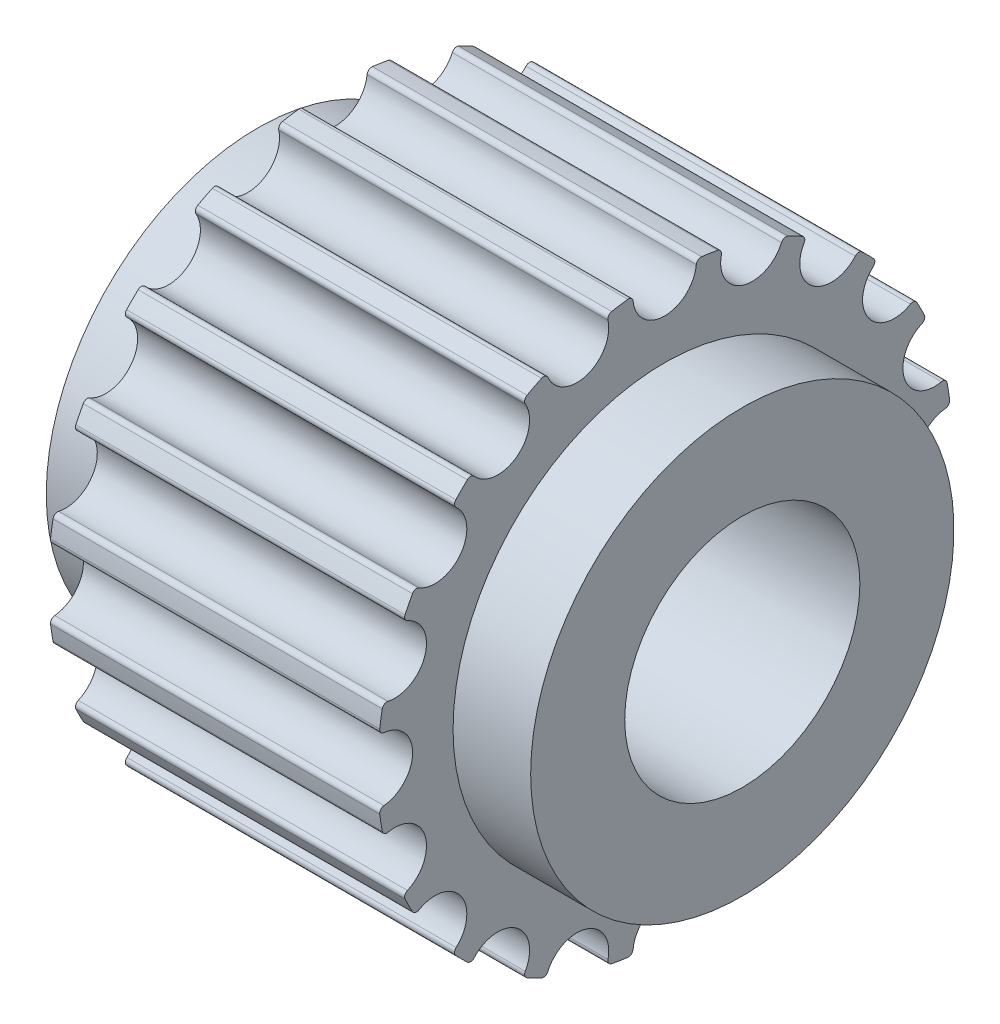
SolidWorks part; units mm, degrees
ref_plane "Front Plane" through (0, 0, 0) normal (0, 0, 1) x (1, 0, 0)
ref_plane "Top Plane" through (0, 0, 0) normal (0, 1, 0) x (1, 0, 0)
ref_plane "Right Plane" through (0, 0, 0) normal (1, 0, 0) x (0, 0, -1)
sketch "Sketch1" plane through (0, 0, 0) normal (0, 0, 1) x (1, 0, 0)
  line L0 (1.65, 6.365) -> (8.65, 6.365) construction
  line L1 (1.65, 6.11) -> (8.65, 6.11)
  line L2 (0, 4.5) -> (0, 2.5)
  line L4 (10.3, 4.5) -> (10.3, 2.5)
  line L5 (0, 2.5) -> (10.3, 2.5)
  line L6 (0, 0) -> (10.3, 0) construction
  line L8 (1.65, 4.5) -> (0, 4.5)
  line L9 (8.65, 4.5) -> (8.65, 6.11)
  line L10 (10.3, 4.5) -> (8.65, 4.5)
  line L13 (1.65, 4.5) -> (1.65, 6.11)
  dimension "W" = 10.3
  dimension "A" = 7
  dimension "E" = 9
  dimension "H" = 5
revolve "Revolve1" add sketch "Sketch1" angle 360 about L6
sketch "Sketch2" plane through (1.65, 0, 0) normal (1, 0, 0) x (0, 0, -1)
  line L0 (0, 0) -> (0, 6.11) construction
  circle A0 centre (0, 0) radius 6.11 construction
  circle A1 centre (0, 0) radius 6.11 construction
  arc A2 (0.6739, 6.0727) -> (-0.6739, 6.0727) centre (0, 0) ccw
  arc A3 (-0.6739, 6.0727) -> (0.6739, 6.0727) centre (0, 6.035) ccw
  circle A6 centre (0, 0) radius 5.36 construction
  circle A7 centre (0, 0) radius 6.364 construction
  dimension "MSM_3" = 0.675
  dimension "MSM_2" = 0.254
  dimension "MSM_1" = 0.75
extrude "Cut-Extrude1" cut sketch "Sketch2" along normal through all
fillet "Fillet1" radius 0.1 2 edges at (5.15, 6.0727, -0.6739) (5.15, 6.0727, 0.6739)
pattern_circular "CirPattern1" count 20 over 360 about axis through (0, 0, 0) along (1, 0, 0) of "Cut-Extrude1", "Fillet1"
hole_wizard "Tapped Hole2" [suppressed] positions "Sketch9" profile "Sketch8" tap size "M3x0.5" standard "JIS"
sketch "Sketch9" [suppressed] plane through (10.3, 8.8848, 0.534) normal (1, 0, 0) x (0, 0, -1)
  line L2 (0.534, -8.8848) -> (0.534, -16.8848) construction
  line L3 (0.534, -8.8848) -> (-6.3942, -4.8848) construction
  circle A0 centre (0.534, -8.8848) radius 8 construction
  point P0 (0.534, -16.8848)
  point P23 (-6.3942, -4.8848)
  point P24 (7.4622, -4.8848)
  dimension "QTC" = 16
  dimension "Angle_2" = 120
  dimension "Number" = 3
sketch "Sketch8" [suppressed] plane through (10.3, -8, 0) normal (0, 1, 0) x (0, 0, -1)
  line L0 (0, 0) -> (0, 9.2511)
  line L1 (0, 9.2511) -> (1.25, 8.5)
  line L2 (1.25, 8.5) -> (1.25, 0)
  line L5 (1.25, 0) -> (0, 0)
  line L10 (0, 9.2511) -> (-1.25, 8.5) construction
  line L11 (0, 0) -> (0, 9.2511) construction
  dimension "Tap Drill Dia." = 2.5
  dimension "Tap Drill Depth" = 8.5
  dimension "Drill Angle" = 118
cosmetic thread "Hole Thread2" [suppressed] parameters "Mx2"=6, "M"=3
cosmetic thread "Hole Thread3" [suppressed] parameters "Mx2"=6, "M"=3
cosmetic thread "Hole Thread4" [suppressed] parameters "Mx2"=6, "M"=3
hole_wizard "Tapped Hole3" [suppressed] positions "Sketch11" profile "Sketch10" tap size "M3x0.5" standard "JIS"
sketch "Sketch11" [suppressed] plane through (10.3, 6.1168, -5.003) normal (1, 0, 0) x (0, 0, -1)
  line L3 (-5.003, -6.1168) -> (-10.6598, -11.7737) construction
  line L4 (-5.003, -6.1168) -> (-10.6598, -0.46) construction
  line L5 (-5.003, 1.8832) -> (-5.003, -14.1168) construction
  circle A0 centre (-5.003, -6.1168) radius 8 construction
  point P22 (-10.6598, -11.7737)
  point P23 (6.0104, 6.0104)
  point P27 (-10.6598, -0.46)
  point P28 (0.6539, -0.46)
  point P29 (0.6539, -11.7737)
  dimension "QFC" = 16
  dimension "Angle_2" = 90
  dimension "Angle_1" = 45
  dimension "Number" = 4
sketch "Sketch10" [suppressed] plane through (10.3, -5.6569, 5.6569) normal (0, 1, 0) x (0, 0, -1)
  line L0 (0, 0) -> (0, 9.2511)
  line L1 (0, 9.2511) -> (1.25, 8.5)
  line L2 (1.25, 8.5) -> (1.25, 0)
  line L5 (1.25, 0) -> (0, 0)
  line L10 (0, 9.2511) -> (-1.25, 8.5) construction
  line L11 (0, 0) -> (0, 9.2511) construction
  dimension "Tap Drill Dia." = 2.5
  dimension "Tap Drill Depth" = 8.5
  dimension "Drill Angle" = 118
cosmetic thread "Hole Thread5" [suppressed] parameters "Mx2"=6, "M"=3
cosmetic thread "Hole Thread6" [suppressed] parameters "Mx2"=6, "M"=3
cosmetic thread "Hole Thread7" [suppressed] parameters "Mx2"=6, "M"=3
cosmetic thread "Hole Thread8" [suppressed] parameters "Mx2"=6, "M"=3
hole_wizard "Tapped Hole4" [suppressed] positions "Sketch13" profile "Sketch12" tap size "M3x0.5" standard "JIS"
sketch "Sketch13" [suppressed] plane through (10.3, 0, 0) normal (1, 0, 0) x (0, 0, -1)
  line L0 (0, 0) -> (0, 8) construction
  line L2 (0, 0) -> (-3.3809, 7.2505) construction
  line L4 (0, 0) -> (4.5886, 6.5532) construction
  circle A0 centre (0, 0) radius 8 construction
  point P0 (-3.3809, 7.2505)
  point P33 (4.5886, 6.5532)
  point P34 (7.9696, -0.6972)
  point P35 (3.3809, -7.2505)
  point P36 (-4.5886, -6.5532)
  point P37 (-7.9696, 0.6972)
  point P38 (0, 0)
  dimension "QSC" = 16
  dimension "Angle_1" = 35
  dimension "Angle_2" = 60
  dimension "Number" = 6
sketch "Sketch12" [suppressed] plane through (10.3, 7.2505, 3.3809) normal (0, 1, 0) x (0, 0, -1)
  line L0 (0, 0) -> (0, 9.2511)
  line L1 (0, 9.2511) -> (1.25, 8.5)
  line L2 (1.25, 8.5) -> (1.25, 0)
  line L5 (1.25, 0) -> (0, 0)
  line L10 (0, 9.2511) -> (-1.25, 8.5) construction
  line L11 (0, 0) -> (0, 9.2511) construction
  dimension "Tap Drill Dia." = 2.5
  dimension "Tap Drill Depth" = 8.5
  dimension "Drill Angle" = 118
cosmetic thread "Hole Thread9" [suppressed] parameters "Mx2"=6, "M"=3
cosmetic thread "Hole Thread10" [suppressed] parameters "Mx2"=6, "M"=3
cosmetic thread "Hole Thread11" [suppressed] parameters "Mx2"=6, "M"=3
cosmetic thread "Hole Thread12" [suppressed] parameters "Mx2"=6, "M"=3
cosmetic thread "Hole Thread13" [suppressed] parameters "Mx2"=6, "M"=3
cosmetic thread "Hole Thread14" [suppressed] parameters "Mx2"=6, "M"=3
hole_wizard "Diameter Hole1" [suppressed] positions "Sketch15" profile "Sketch14" hole size "Ø4.0" standard "JIS"
sketch "Sketch15" [suppressed] plane through (0, 0, 0) normal (1, 0, 0) x (0, 0, -1)
  line L11 (0, 0) -> (0, -8) construction
  line L12 (0, 0) -> (-6.9282, 4) construction
  circle A2 centre (0, 0) radius 8 construction
  point P16 (0, -8)
  point P80 (-6.9282, 4)
  point P81 (6.9282, 4)
  dimension "D1" = 120
  dimension "KTC" = 16
  dimension "D2" = 3
sketch "Sketch14" [suppressed] plane through (0, -8, 0) normal (0, 1, 0) x (0, 0, 1)
  line L0 (0, 0) -> (0, 10.3)
  line L1 (0, 10.3) -> (2, 10.3)
  line L2 (2, 10.3) -> (2, 0)
  line L5 (2, 0) -> (0, 0)
  line L11 (0, 0) -> (0, 10.3) construction
  dimension "K" = 4
  dimension "Thru Hole Depth" = 10.3
hole_wizard "Diameter Hole2" [suppressed] positions "Sketch17" profile "Sketch16" hole size "Ø4.0" standard "JIS"
sketch "Sketch17" [suppressed] plane through (0, 0, 0) normal (1, 0, 0) x (0, 0, -1)
  line L18 (0, 0) -> (-5.6569, -5.6569) construction
  line L19 (0, 0) -> (-5.6569, 5.6569) construction
  line L20 (0, 8) -> (0, -8) construction
  circle A2 centre (0, 0) radius 8 construction
  point P104 (-5.6569, -5.6569)
  point P120 (-6.364, 6.364)
  point P146 (-5.6569, 5.6569)
  point P147 (5.6569, 5.6569)
  point P148 (5.6569, -5.6569)
  dimension "D1" = 90
  dimension "KFC" = 16
  dimension "D2" = 45
  dimension "D3" = 4
sketch "Sketch16" [suppressed] plane through (0, -5.6569, 5.6569) normal (0, 1, 0) x (0, 0, 1)
  line L0 (0, 0) -> (0, 10.3)
  line L1 (0, 10.3) -> (2, 10.3)
  line L2 (2, 10.3) -> (2, 0)
  line L5 (2, 0) -> (0, 0)
  line L11 (0, 0) -> (0, 10.3) construction
  dimension "K" = 4
  dimension "Thru Hole Depth" = 10.3
hole_wizard "Diameter Hole3" [suppressed] positions "Sketch19" profile "Sketch18" hole size "Ø4.0" standard "JIS"
sketch "Sketch19" [suppressed] plane through (0, 0, 0) normal (-1, 0, 0) x (0, 0, 1)
  line L0 (0, 8) -> (0, 0) construction
  line L1 (0, 0) -> (3.3809, 7.2505) construction
  line L3 (0, 0) -> (-4.5886, 6.5532) construction
  circle A0 centre (0, 0) radius 8 construction
  point P0 (-4.5886, 6.5532)
  point P23 (3.3809, 7.2505)
  point P24 (7.9696, 0.6972)
  point P25 (4.5886, -6.5532)
  point P26 (-3.3809, -7.2505)
  point P27 (-7.9696, -0.6972)
  point P28 (0, 0)
  dimension "D3" = 6
  dimension "KSC" = 16
  dimension "D1" = 35
  dimension "D2" = 60
sketch "Sketch18" [suppressed] plane through (0, 6.5532, -4.5886) normal (0, 1, 0) x (0, 0, 1)
  line L0 (0, 0) -> (0, 10.3)
  line L1 (0, 10.3) -> (2, 10.3)
  line L2 (2, 10.3) -> (2, 0)
  line L5 (2, 0) -> (0, 0)
  line L11 (0, 0) -> (0, 10.3) construction
  dimension "K" = 4
  dimension "Thru Hole Depth" = 10.3
hole_wizard "CBORE for Socket Head Cap Screw1" [suppressed] positions "Sketch21" profile "Sketch20" counterbore size "M3" standard "JIS"
sketch "Sketch21" [suppressed] plane through (0, 0, 0) normal (-1, 0, 0) x (0, 0, 1)
  line L2 (0, 0) -> (0, -9.25) construction
  line L4 (0, 0) -> (8.0107, 4.625) construction
  circle A0 centre (0, 0) radius 9.25 construction
  circle A1 centre (8.0107, 4.625) radius 1.5 construction
  point P0 (0, -9.25)
  point P38 (-8.0107, 4.625)
  point P39 (8.0107, 4.625)
  dimension "ZTC" = 18.5
  dimension "D2" = 120
  dimension "D1" = 3
  dimension "ZM" = 3
sketch "Sketch20" [suppressed] plane through (0, -9.25, 0) normal (0, 1, 0) x (0, 0, 1)
  line L0 (0, 0) -> (0, 10.3)
  line L1 (0, 10.3) -> (1.7, 10.3)
  line L3 (1.7, 10.3) -> (1.7, 3)
  line L4 (1.7, 3) -> (3.25, 3)
  line L5 (3.25, 3) -> (3.25, 0)
  line L7 (3.25, 0) -> (0, 0)
  line L11 (0, 0) -> (0, 10.3) construction
  dimension "D1_s" = 3.4
  dimension "Thru Hole Depth" = 10.3
  dimension "D2_s" = 6.5
  dimension "H_s" = 3
hole_wizard "CBORE for Socket Head Cap Screw2" [suppressed] positions "Sketch23" profile "Sketch22" counterbore size "M3" standard "JIS"
sketch "Sketch23" [suppressed] plane through (0, 0, 0) normal (-1, 0, 0) x (0, 0, 1)
  line L0 (0, 0) -> (0, 9.25) construction
  line L2 (6.5407, 6.5407) -> (0, 0) construction
  line L3 (0, 0) -> (6.5407, -6.5407) construction
  circle A0 centre (0, 0) radius 9.25 construction
  circle A1 centre (6.5407, 6.5407) radius 1.5 construction
  point P0 (6.5407, 6.5407)
  point P31 (6.5407, -6.5407)
  point P32 (-6.5407, -6.5407)
  point P33 (-6.5407, 6.5407)
  dimension "ZFC" = 18.5
  dimension "D2" = 45
  dimension "D3" = 90
  dimension "D1" = 4
  dimension "ZM" = 3
sketch "Sketch22" [suppressed] plane through (0, 6.5407, 6.5407) normal (0, 1, 0) x (0, 0, 1)
  line L0 (0, 0) -> (0, 10.3)
  line L1 (0, 10.3) -> (1.75, 10.3)
  line L3 (1.75, 10.3) -> (1.75, 3.5)
  line L4 (1.75, 3.5) -> (3.25, 3.5)
  line L5 (3.25, 3.5) -> (3.25, 0)
  line L7 (3.25, 0) -> (0, 0)
  line L11 (0, 0) -> (0, 10.3) construction
  dimension "D1_s" = 3.5
  dimension "Thru Hole Depth" = 10.3
  dimension "D2_s" = 6.5
  dimension "H_s" = 3.5
hole_wizard "CBORE for Socket Head Cap Screw3" [suppressed] positions "Sketch25" profile "Sketch24" counterbore size "M3" standard "JIS"
sketch "Sketch25" [suppressed] plane through (0, 0, 0) normal (-1, 0, 0) x (0, 0, 1)
  line L0 (0, 0) -> (0, 9.25) construction
  line L2 (0, 0) -> (-5.3056, 7.5772) construction
  line L4 (0, 0) -> (3.9092, 8.3833) construction
  circle A0 centre (0, 0) radius 9.25 construction
  circle A1 centre (3.9092, 8.3833) radius 1.5 construction
  point P0 (-5.3056, 7.5772)
  point P32 (3.9092, 8.3833)
  point P33 (9.2148, 0.8062)
  point P34 (5.3056, -7.5772)
  point P35 (-3.9092, -8.3833)
  point P36 (-9.2148, -0.8062)
  dimension "ZSC" = 18.5
  dimension "D2" = 35
  dimension "D3" = 60
  dimension "D1" = 6
  dimension "ZM" = 3
sketch "Sketch24" [suppressed] plane through (0, 7.5772, -5.3056) normal (0, 1, 0) x (0, 0, 1)
  line L0 (0, 0) -> (0, 10.3)
  line L1 (0, 10.3) -> (1.75, 10.3)
  line L3 (1.75, 10.3) -> (1.75, 3.5)
  line L4 (1.75, 3.5) -> (3.25, 3.5)
  line L5 (3.25, 3.5) -> (3.25, 0)
  line L7 (3.25, 0) -> (0, 0)
  line L11 (0, 0) -> (0, 10.3) construction
  dimension "D1_s" = 3.5
  dimension "Thru Hole Depth" = 10.3
  dimension "D2_s" = 6.5
  dimension "H_s" = 3.5
equation "\"Plane dim\"= \"O.D.@Sketch1\" * 0.5"
equation "\"ZM\"=3.000000"
